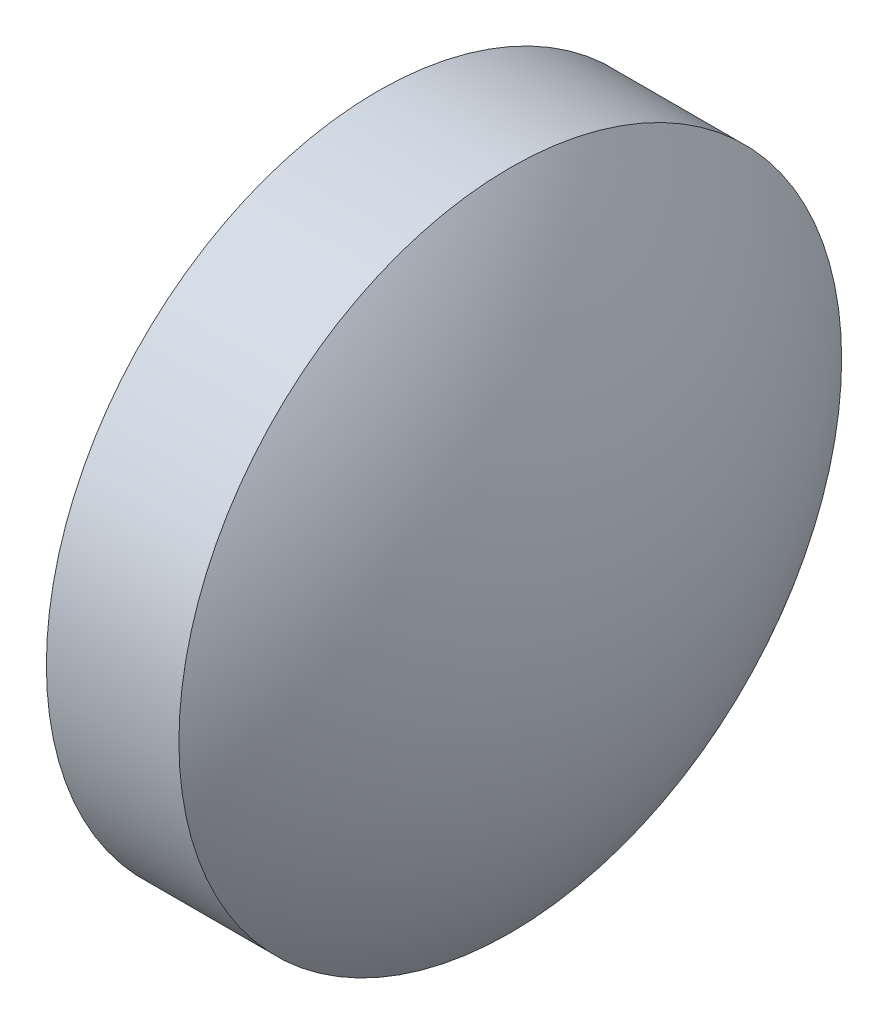
SolidWorks part; units mm, degrees
ref_plane "前视基准面" through (0, 0, 0) normal (0, 0, 1) x (1, 0, 0)
ref_plane "上视基准面" through (0, 0, 0) normal (0, 1, 0) x (1, 0, 0)
ref_plane "右视基准面" through (0, 0, 0) normal (1, 0, 0) x (0, 0, -1)
sketch "草图1" plane through (0, 0, 0) normal (0, 0, 1) x (1, 0, 0)
  line L0 (16.5193, 12.0701) -> (17.5193, 12.0701)
  line L1 (17.5193, 12.0701) -> (17.5193, 7.0701)
  line L2 (17.5193, 7.0701) -> (16.5193, 7.0701)
  line L3 (16.5193, 7.0701) -> (16.5193, 12.0701)
  line L4 (15.2362, 9.5701) -> (18.7927, 9.5701) construction
  arc A0 (16.5193, 12.0701) -> (16.5193, 7.0701) centre (19.8967, 9.5701) ccw
  arc A1 (17.5193, 7.0701) -> (17.5193, 12.0701) centre (14.142, 9.5701) ccw
  dimension "D1" = 1
  dimension "D2" = 5
revolve "旋转1" add sketch "草图1" angle 360 about L4
